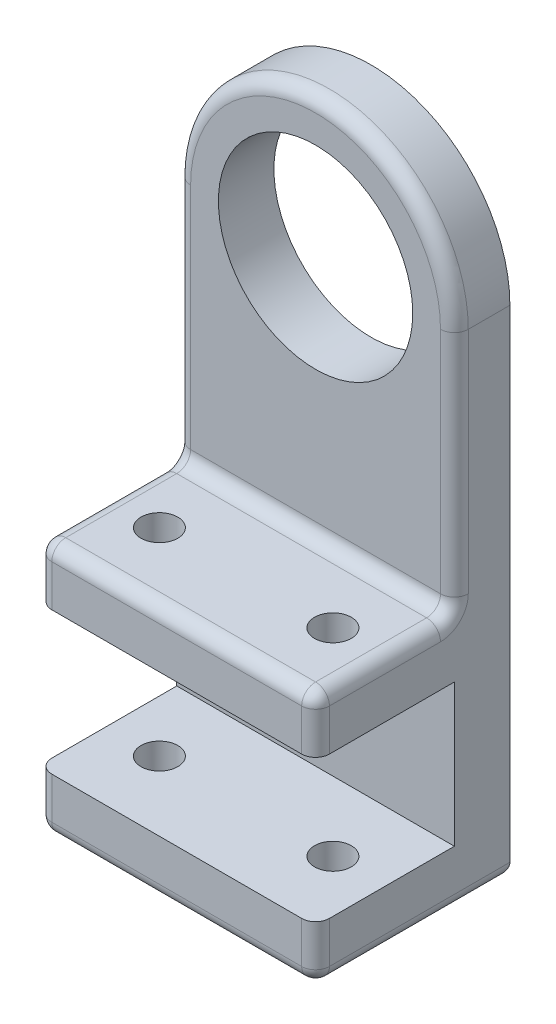
SolidWorks part; units mm, degrees
ref_plane "Front Plane" through (0, 0, 0) normal (0, 0, 1) x (1, 0, 0)
ref_plane "Top Plane" through (0, 0, 0) normal (0, 1, 0) x (1, 0, 0)
ref_plane "Right Plane" through (0, 0, 0) normal (1, 0, 0) x (0, 0, -1)
sketch "Sketch1" plane through (0, 0, 0) normal (0, 0, 1) x (1, 0, 0)
  line L0 (-20, 0) -> (-20, -71.5)
  line L1 (-20, -71.5) -> (20, -71.5)
  line L2 (20, -71.5) -> (20, 0)
  arc A0 (-20, 0) -> (20, 0) centre (0, 0) cw
  circle A1 centre (0, 0) radius 14
  dimension "D1" = 20
  dimension "D3" = 28
  dimension "D2" = 71.5
extrude "Boss-Extrude1" add sketch "Sketch1" along normal blind 8
sketch "Sketch2" plane through (0, 0, 8) normal (0, 0, 1) x (1, 0, 0)
  line L0 (-20, 0) -> (-20, -71.5) construction
  line L1 (-20, -35) -> (20, -35)
  line L2 (-20, -35) -> (-20, -43)
  line L3 (-20, -43) -> (20, -43)
  line L4 (20, -35) -> (20, -43)
  line L5 (20, -71.5) -> (20, 0) construction
  line L7 (20, -71.5) -> (-20, -71.5)
  line L8 (20, -71.5) -> (20, -63.5)
  line L9 (20, -63.5) -> (-20, -63.5)
  line L10 (-20, -71.5) -> (-20, -63.5)
  dimension "D1" = 8
  dimension "D2" = 20.5
extrude "Boss-Extrude2" add sketch "Sketch2" along normal blind 20
sketch "Sketch3" plane through (0, -35, 0) normal (0, 1, 0) x (1, 0, 0)
  line L0 (-20, -18) -> (20, -18) construction
  line L1 (-20, -28) -> (-20, -8) construction
  line L2 (20, -28) -> (20, -8) construction
  line L3 (20, -18) -> (0, -28) construction
  line L4 (20, -28) -> (-20, -28) construction
  line L5 (0, -28) -> (0, -8) construction
  line L6 (20, -8) -> (-20, -8) construction
  circle A0 centre (-12.5, -18) radius 2.65
  circle A1 centre (12.5, -18) radius 2.65
  point P16 (0, 0)
  dimension "D1" = 5.3
  dimension "D2" = 25
extrude "Cut-Extrude1" cut sketch "Sketch3" against normal through all
fillet "Fillet1" radius 2 15 edges at (0, -71.5, 0) (0, -35, 8) (-20, -35, 18) (-20, -17.5, 8) (0, 20, 8) (20, -17.5, 8) (0, -35, 28) (20, -35, 18) (-20, -71.5, 14) (0, -71.5, 28) (20, -71.5, 14) (20, -67.5, 28) (-20, -67.5, 28) (20, -39, 28) (-20, -39, 28)
